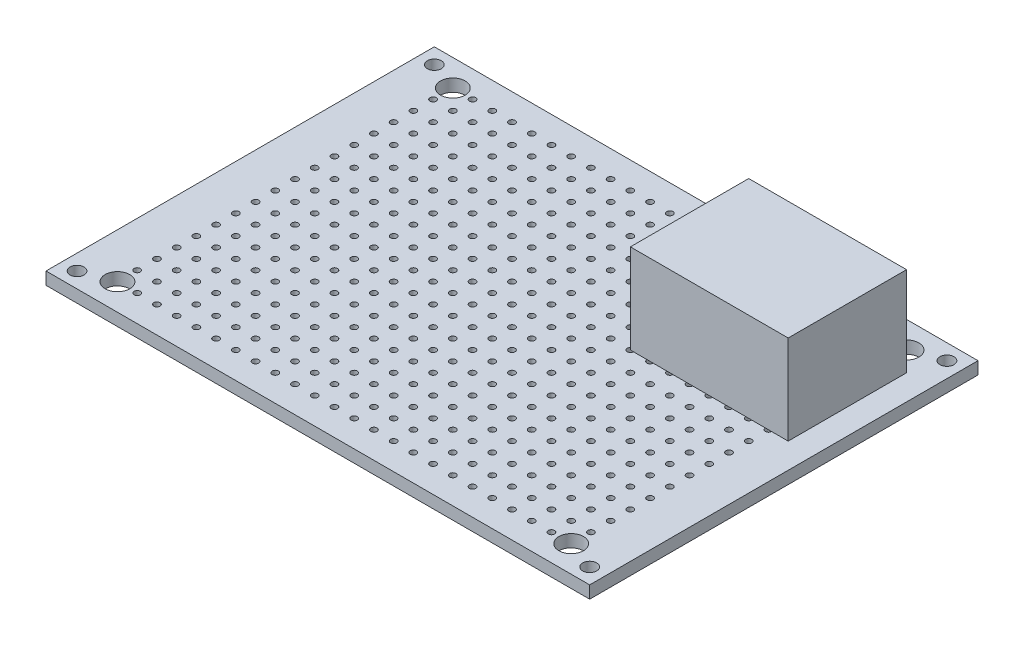
SolidWorks part; units mm, degrees
ref_plane "Front Plane" through (0, 0, 0) normal (0, 0, 1) x (1, 0, 0)
ref_plane "Top Plane" through (0, 0, 0) normal (0, 1, 0) x (1, 0, 0)
ref_plane "Right Plane" through (0, 0, 0) normal (1, 0, 0) x (0, 0, -1)
sketch "Sketch1" plane through (0, 0, 0) normal (0, 1, 0) x (1, 0, 0)
  line L1 (-35, -25) -> (35, -25)
  line L2 (-35, -25) -> (-35, 25)
  line L3 (-35, 25) -> (35, 25)
  line L4 (35, -25) -> (35, 25)
  line L5 (-35, -25) -> (35, 25) construction
  line L6 (-35, 25) -> (35, -25) construction
  point P0 (0, 0)
  dimension "D1" = 50
  dimension "D2" = 70
extrude "Boss-Extrude1" add sketch "Sketch1" along normal blind 1.6
sketch "Sketch2" plane through (0, 1.6, 0) normal (0, 1, 0) x (1, 0, 0)
  line L1 (-33, -23) -> (33, -23) construction
  line L2 (-33, -23) -> (-33, 23) construction
  line L3 (-33, 23) -> (33, 23) construction
  line L4 (33, -23) -> (33, 23) construction
  line L5 (-33, -23) -> (33, 23) construction
  line L6 (-33, 23) -> (33, -23) construction
  circle A0 centre (-33, 23) radius 0.9
  circle A1 centre (-33, -23) radius 0.9
  circle A2 centre (33, -23) radius 0.9
  circle A3 centre (33, 23) radius 0.9
  point P0 (0, 0)
  dimension "D3" = 1.8
  dimension "D1" = 46
  dimension "D2" = 66
extrude "Cut-Extrude1" cut sketch "Sketch2" against normal through all
sketch "Sketch3" plane through (0, 1.6, 0) normal (0, 1, 0) x (1, 0, 0)
  line L0 (-29.21, -21.59) -> (-26.67, -21.59) construction
  line L1 (29.21, -21.59) -> (-29.21, -21.59) construction
  line L2 (29.21, -21.59) -> (29.21, 21.59) construction
  line L3 (29.21, 21.59) -> (-29.21, 21.59) construction
  line L4 (-29.21, -21.59) -> (-29.21, 21.59) construction
  line L5 (29.21, -21.59) -> (-29.21, 21.59) construction
  line L6 (29.21, 21.59) -> (-29.21, -21.59) construction
  line L7 (-29.21, -21.59) -> (-29.21, -19.05) construction
  circle A0 centre (-29.21, -21.59) radius 0.4
  circle A1 centre (-26.67, -21.59) radius 0.4
  circle A2 centre (-24.13, -21.59) radius 0.4
  circle A3 centre (-21.59, -21.59) radius 0.4
  circle A4 centre (-19.05, -21.59) radius 0.4
  circle A5 centre (-16.51, -21.59) radius 0.4
  circle A6 centre (-13.97, -21.59) radius 0.4
  circle A7 centre (-11.43, -21.59) radius 0.4
  circle A8 centre (-8.89, -21.59) radius 0.4
  circle A9 centre (-6.35, -21.59) radius 0.4
  circle A10 centre (-3.81, -21.59) radius 0.4
  circle A11 centre (-1.27, -21.59) radius 0.4
  circle A12 centre (1.27, -21.59) radius 0.4
  circle A13 centre (3.81, -21.59) radius 0.4
  circle A14 centre (6.35, -21.59) radius 0.4
  circle A15 centre (8.89, -21.59) radius 0.4
  circle A16 centre (11.43, -21.59) radius 0.4
  circle A17 centre (13.97, -21.59) radius 0.4
  circle A18 centre (16.51, -21.59) radius 0.4
  circle A19 centre (19.05, -21.59) radius 0.4
  circle A20 centre (21.59, -21.59) radius 0.4
  circle A21 centre (24.13, -21.59) radius 0.4
  circle A22 centre (26.67, -21.59) radius 0.4
  circle A23 centre (29.21, -21.59) radius 0.4
  circle A24 centre (-26.67, -19.05) radius 0.4
  circle A25 centre (-24.13, -19.05) radius 0.4
  circle A26 centre (-21.59, -19.05) radius 0.4
  circle A27 centre (-19.05, -19.05) radius 0.4
  circle A28 centre (-16.51, -19.05) radius 0.4
  circle A29 centre (-13.97, -19.05) radius 0.4
  circle A30 centre (-11.43, -19.05) radius 0.4
  circle A31 centre (-8.89, -19.05) radius 0.4
  circle A32 centre (-6.35, -19.05) radius 0.4
  circle A33 centre (-3.81, -19.05) radius 0.4
  circle A34 centre (-1.27, -19.05) radius 0.4
  circle A35 centre (1.27, -19.05) radius 0.4
  circle A36 centre (3.81, -19.05) radius 0.4
  circle A37 centre (6.35, -19.05) radius 0.4
  circle A38 centre (8.89, -19.05) radius 0.4
  circle A39 centre (11.43, -19.05) radius 0.4
  circle A40 centre (13.97, -19.05) radius 0.4
  circle A41 centre (16.51, -19.05) radius 0.4
  circle A42 centre (19.05, -19.05) radius 0.4
  circle A43 centre (21.59, -19.05) radius 0.4
  circle A44 centre (24.13, -19.05) radius 0.4
  circle A45 centre (26.67, -19.05) radius 0.4
  circle A46 centre (29.21, -19.05) radius 0.4
  circle A47 centre (-26.67, -16.51) radius 0.4
  circle A48 centre (-24.13, -16.51) radius 0.4
  circle A49 centre (-21.59, -16.51) radius 0.4
  circle A50 centre (-19.05, -16.51) radius 0.4
  circle A51 centre (-16.51, -16.51) radius 0.4
  circle A52 centre (-13.97, -16.51) radius 0.4
  circle A53 centre (-11.43, -16.51) radius 0.4
  circle A54 centre (-8.89, -16.51) radius 0.4
  circle A55 centre (-6.35, -16.51) radius 0.4
  circle A56 centre (-3.81, -16.51) radius 0.4
  circle A57 centre (-1.27, -16.51) radius 0.4
  circle A58 centre (1.27, -16.51) radius 0.4
  circle A59 centre (3.81, -16.51) radius 0.4
  circle A60 centre (6.35, -16.51) radius 0.4
  circle A61 centre (8.89, -16.51) radius 0.4
  circle A62 centre (11.43, -16.51) radius 0.4
  circle A63 centre (13.97, -16.51) radius 0.4
  circle A64 centre (16.51, -16.51) radius 0.4
  circle A65 centre (19.05, -16.51) radius 0.4
  circle A66 centre (21.59, -16.51) radius 0.4
  circle A67 centre (24.13, -16.51) radius 0.4
  circle A68 centre (26.67, -16.51) radius 0.4
  circle A69 centre (29.21, -16.51) radius 0.4
  circle A70 centre (-26.67, -13.97) radius 0.4
  circle A71 centre (-24.13, -13.97) radius 0.4
  circle A72 centre (-21.59, -13.97) radius 0.4
  circle A73 centre (-19.05, -13.97) radius 0.4
  circle A74 centre (-16.51, -13.97) radius 0.4
  circle A75 centre (-13.97, -13.97) radius 0.4
  circle A76 centre (-11.43, -13.97) radius 0.4
  circle A77 centre (-8.89, -13.97) radius 0.4
  circle A78 centre (-6.35, -13.97) radius 0.4
  circle A79 centre (-3.81, -13.97) radius 0.4
  circle A80 centre (-1.27, -13.97) radius 0.4
  circle A81 centre (1.27, -13.97) radius 0.4
  circle A82 centre (3.81, -13.97) radius 0.4
  circle A83 centre (6.35, -13.97) radius 0.4
  circle A84 centre (8.89, -13.97) radius 0.4
  circle A85 centre (11.43, -13.97) radius 0.4
  circle A86 centre (13.97, -13.97) radius 0.4
  circle A87 centre (16.51, -13.97) radius 0.4
  circle A88 centre (19.05, -13.97) radius 0.4
  circle A89 centre (21.59, -13.97) radius 0.4
  circle A90 centre (24.13, -13.97) radius 0.4
  circle A91 centre (26.67, -13.97) radius 0.4
  circle A92 centre (29.21, -13.97) radius 0.4
  circle A93 centre (-26.67, -11.43) radius 0.4
  circle A94 centre (-24.13, -11.43) radius 0.4
  circle A95 centre (-21.59, -11.43) radius 0.4
  circle A96 centre (-19.05, -11.43) radius 0.4
  circle A97 centre (-16.51, -11.43) radius 0.4
  circle A98 centre (-13.97, -11.43) radius 0.4
  circle A99 centre (-11.43, -11.43) radius 0.4
  circle A100 centre (-8.89, -11.43) radius 0.4
  circle A101 centre (-6.35, -11.43) radius 0.4
  circle A102 centre (-3.81, -11.43) radius 0.4
  circle A103 centre (-1.27, -11.43) radius 0.4
  circle A104 centre (1.27, -11.43) radius 0.4
  circle A105 centre (3.81, -11.43) radius 0.4
  circle A106 centre (6.35, -11.43) radius 0.4
  circle A107 centre (8.89, -11.43) radius 0.4
  circle A108 centre (11.43, -11.43) radius 0.4
  circle A109 centre (13.97, -11.43) radius 0.4
  circle A110 centre (16.51, -11.43) radius 0.4
  circle A111 centre (19.05, -11.43) radius 0.4
  circle A112 centre (21.59, -11.43) radius 0.4
  circle A113 centre (24.13, -11.43) radius 0.4
  circle A114 centre (26.67, -11.43) radius 0.4
  circle A115 centre (29.21, -11.43) radius 0.4
  circle A116 centre (-26.67, -8.89) radius 0.4
  circle A117 centre (-24.13, -8.89) radius 0.4
  circle A118 centre (-21.59, -8.89) radius 0.4
  circle A119 centre (-19.05, -8.89) radius 0.4
  circle A120 centre (-16.51, -8.89) radius 0.4
  circle A121 centre (-13.97, -8.89) radius 0.4
  circle A122 centre (-11.43, -8.89) radius 0.4
  circle A123 centre (-8.89, -8.89) radius 0.4
  circle A124 centre (-6.35, -8.89) radius 0.4
  circle A125 centre (-3.81, -8.89) radius 0.4
  circle A126 centre (-1.27, -8.89) radius 0.4
  circle A127 centre (1.27, -8.89) radius 0.4
  circle A128 centre (3.81, -8.89) radius 0.4
  circle A129 centre (6.35, -8.89) radius 0.4
  circle A130 centre (8.89, -8.89) radius 0.4
  circle A131 centre (11.43, -8.89) radius 0.4
  circle A132 centre (13.97, -8.89) radius 0.4
  circle A133 centre (16.51, -8.89) radius 0.4
  circle A134 centre (19.05, -8.89) radius 0.4
  circle A135 centre (21.59, -8.89) radius 0.4
  circle A136 centre (24.13, -8.89) radius 0.4
  circle A137 centre (26.67, -8.89) radius 0.4
  circle A138 centre (29.21, -8.89) radius 0.4
  circle A139 centre (-26.67, -6.35) radius 0.4
  circle A140 centre (-24.13, -6.35) radius 0.4
  circle A141 centre (-21.59, -6.35) radius 0.4
  circle A142 centre (-19.05, -6.35) radius 0.4
  circle A143 centre (-16.51, -6.35) radius 0.4
  circle A144 centre (-13.97, -6.35) radius 0.4
  circle A145 centre (-11.43, -6.35) radius 0.4
  circle A146 centre (-8.89, -6.35) radius 0.4
  circle A147 centre (-6.35, -6.35) radius 0.4
  circle A148 centre (-3.81, -6.35) radius 0.4
  circle A149 centre (-1.27, -6.35) radius 0.4
  circle A150 centre (1.27, -6.35) radius 0.4
  circle A151 centre (3.81, -6.35) radius 0.4
  circle A152 centre (6.35, -6.35) radius 0.4
  circle A153 centre (8.89, -6.35) radius 0.4
  circle A154 centre (11.43, -6.35) radius 0.4
  circle A155 centre (13.97, -6.35) radius 0.4
  circle A156 centre (16.51, -6.35) radius 0.4
  circle A157 centre (19.05, -6.35) radius 0.4
  circle A158 centre (21.59, -6.35) radius 0.4
  circle A159 centre (24.13, -6.35) radius 0.4
  circle A160 centre (26.67, -6.35) radius 0.4
  circle A161 centre (29.21, -6.35) radius 0.4
  circle A162 centre (-26.67, -3.81) radius 0.4
  circle A163 centre (-24.13, -3.81) radius 0.4
  circle A164 centre (-21.59, -3.81) radius 0.4
  circle A165 centre (-19.05, -3.81) radius 0.4
  circle A166 centre (-16.51, -3.81) radius 0.4
  circle A167 centre (-13.97, -3.81) radius 0.4
  circle A168 centre (-11.43, -3.81) radius 0.4
  circle A169 centre (-8.89, -3.81) radius 0.4
  circle A170 centre (-6.35, -3.81) radius 0.4
  circle A171 centre (-3.81, -3.81) radius 0.4
  circle A172 centre (-1.27, -3.81) radius 0.4
  circle A173 centre (1.27, -3.81) radius 0.4
  circle A174 centre (3.81, -3.81) radius 0.4
  circle A175 centre (6.35, -3.81) radius 0.4
  circle A176 centre (8.89, -3.81) radius 0.4
  circle A177 centre (11.43, -3.81) radius 0.4
  circle A178 centre (13.97, -3.81) radius 0.4
  circle A179 centre (16.51, -3.81) radius 0.4
  circle A180 centre (19.05, -3.81) radius 0.4
  circle A181 centre (21.59, -3.81) radius 0.4
  circle A182 centre (24.13, -3.81) radius 0.4
  circle A183 centre (26.67, -3.81) radius 0.4
  circle A184 centre (29.21, -3.81) radius 0.4
  circle A185 centre (-26.67, -1.27) radius 0.4
  circle A186 centre (-24.13, -1.27) radius 0.4
  circle A187 centre (-21.59, -1.27) radius 0.4
  circle A188 centre (-19.05, -1.27) radius 0.4
  circle A189 centre (-16.51, -1.27) radius 0.4
  circle A190 centre (-13.97, -1.27) radius 0.4
  circle A191 centre (-11.43, -1.27) radius 0.4
  circle A192 centre (-8.89, -1.27) radius 0.4
  circle A193 centre (-6.35, -1.27) radius 0.4
  circle A194 centre (-3.81, -1.27) radius 0.4
  circle A195 centre (-1.27, -1.27) radius 0.4
  circle A196 centre (1.27, -1.27) radius 0.4
  circle A197 centre (3.81, -1.27) radius 0.4
  circle A198 centre (6.35, -1.27) radius 0.4
  circle A199 centre (8.89, -1.27) radius 0.4
  circle A200 centre (11.43, -1.27) radius 0.4
  circle A201 centre (13.97, -1.27) radius 0.4
  circle A202 centre (16.51, -1.27) radius 0.4
  circle A203 centre (19.05, -1.27) radius 0.4
  circle A204 centre (21.59, -1.27) radius 0.4
  circle A205 centre (24.13, -1.27) radius 0.4
  circle A206 centre (26.67, -1.27) radius 0.4
  circle A207 centre (29.21, -1.27) radius 0.4
  circle A208 centre (-26.67, 1.27) radius 0.4
  circle A209 centre (-24.13, 1.27) radius 0.4
  circle A210 centre (-21.59, 1.27) radius 0.4
  circle A211 centre (-19.05, 1.27) radius 0.4
  circle A212 centre (-16.51, 1.27) radius 0.4
  circle A213 centre (-13.97, 1.27) radius 0.4
  circle A214 centre (-11.43, 1.27) radius 0.4
  circle A215 centre (-8.89, 1.27) radius 0.4
  circle A216 centre (-6.35, 1.27) radius 0.4
  circle A217 centre (-3.81, 1.27) radius 0.4
  circle A218 centre (-1.27, 1.27) radius 0.4
  circle A219 centre (1.27, 1.27) radius 0.4
  circle A220 centre (3.81, 1.27) radius 0.4
  circle A221 centre (6.35, 1.27) radius 0.4
  circle A222 centre (8.89, 1.27) radius 0.4
  circle A223 centre (11.43, 1.27) radius 0.4
  circle A224 centre (13.97, 1.27) radius 0.4
  circle A225 centre (16.51, 1.27) radius 0.4
  circle A226 centre (19.05, 1.27) radius 0.4
  circle A227 centre (21.59, 1.27) radius 0.4
  circle A228 centre (24.13, 1.27) radius 0.4
  circle A229 centre (26.67, 1.27) radius 0.4
  circle A230 centre (29.21, 1.27) radius 0.4
  circle A231 centre (-26.67, 3.81) radius 0.4
  circle A232 centre (-24.13, 3.81) radius 0.4
  circle A233 centre (-21.59, 3.81) radius 0.4
  circle A234 centre (-19.05, 3.81) radius 0.4
  circle A235 centre (-16.51, 3.81) radius 0.4
  circle A236 centre (-13.97, 3.81) radius 0.4
  circle A237 centre (-11.43, 3.81) radius 0.4
  circle A238 centre (-8.89, 3.81) radius 0.4
  circle A239 centre (-6.35, 3.81) radius 0.4
  circle A240 centre (-3.81, 3.81) radius 0.4
  circle A241 centre (-1.27, 3.81) radius 0.4
  circle A242 centre (1.27, 3.81) radius 0.4
  circle A243 centre (3.81, 3.81) radius 0.4
  circle A244 centre (6.35, 3.81) radius 0.4
  circle A245 centre (8.89, 3.81) radius 0.4
  circle A246 centre (11.43, 3.81) radius 0.4
  circle A247 centre (13.97, 3.81) radius 0.4
  circle A248 centre (16.51, 3.81) radius 0.4
  circle A249 centre (19.05, 3.81) radius 0.4
  circle A250 centre (21.59, 3.81) radius 0.4
  circle A251 centre (24.13, 3.81) radius 0.4
  circle A252 centre (26.67, 3.81) radius 0.4
  circle A253 centre (29.21, 3.81) radius 0.4
  circle A254 centre (-26.67, 6.35) radius 0.4
  circle A255 centre (-24.13, 6.35) radius 0.4
  circle A256 centre (-21.59, 6.35) radius 0.4
  circle A257 centre (-19.05, 6.35) radius 0.4
  circle A258 centre (-16.51, 6.35) radius 0.4
  circle A259 centre (-13.97, 6.35) radius 0.4
  circle A260 centre (-11.43, 6.35) radius 0.4
  circle A261 centre (-8.89, 6.35) radius 0.4
  circle A262 centre (-6.35, 6.35) radius 0.4
  circle A263 centre (-3.81, 6.35) radius 0.4
  circle A264 centre (-1.27, 6.35) radius 0.4
  circle A265 centre (1.27, 6.35) radius 0.4
  circle A266 centre (3.81, 6.35) radius 0.4
  circle A267 centre (6.35, 6.35) radius 0.4
  circle A268 centre (8.89, 6.35) radius 0.4
  circle A269 centre (11.43, 6.35) radius 0.4
  circle A270 centre (13.97, 6.35) radius 0.4
  circle A271 centre (16.51, 6.35) radius 0.4
  circle A272 centre (19.05, 6.35) radius 0.4
  circle A273 centre (21.59, 6.35) radius 0.4
  circle A274 centre (24.13, 6.35) radius 0.4
  circle A275 centre (26.67, 6.35) radius 0.4
  circle A276 centre (29.21, 6.35) radius 0.4
  circle A277 centre (-26.67, 8.89) radius 0.4
  circle A278 centre (-24.13, 8.89) radius 0.4
  circle A279 centre (-21.59, 8.89) radius 0.4
  circle A280 centre (-19.05, 8.89) radius 0.4
  circle A281 centre (-16.51, 8.89) radius 0.4
  circle A282 centre (-13.97, 8.89) radius 0.4
  circle A283 centre (-11.43, 8.89) radius 0.4
  circle A284 centre (-8.89, 8.89) radius 0.4
  circle A285 centre (-6.35, 8.89) radius 0.4
  circle A286 centre (-3.81, 8.89) radius 0.4
  circle A287 centre (-1.27, 8.89) radius 0.4
  circle A288 centre (1.27, 8.89) radius 0.4
  circle A289 centre (3.81, 8.89) radius 0.4
  circle A290 centre (6.35, 8.89) radius 0.4
  circle A291 centre (8.89, 8.89) radius 0.4
  circle A292 centre (11.43, 8.89) radius 0.4
  circle A293 centre (13.97, 8.89) radius 0.4
  circle A294 centre (16.51, 8.89) radius 0.4
  circle A295 centre (19.05, 8.89) radius 0.4
  circle A296 centre (21.59, 8.89) radius 0.4
  circle A297 centre (24.13, 8.89) radius 0.4
  circle A298 centre (26.67, 8.89) radius 0.4
  circle A299 centre (29.21, 8.89) radius 0.4
  circle A300 centre (-26.67, 11.43) radius 0.4
  circle A301 centre (-24.13, 11.43) radius 0.4
  circle A302 centre (-21.59, 11.43) radius 0.4
  circle A303 centre (-19.05, 11.43) radius 0.4
  circle A304 centre (-16.51, 11.43) radius 0.4
  circle A305 centre (-13.97, 11.43) radius 0.4
  circle A306 centre (-11.43, 11.43) radius 0.4
  circle A307 centre (-8.89, 11.43) radius 0.4
  circle A308 centre (-6.35, 11.43) radius 0.4
  circle A309 centre (-3.81, 11.43) radius 0.4
  circle A310 centre (-1.27, 11.43) radius 0.4
  circle A311 centre (1.27, 11.43) radius 0.4
  circle A312 centre (3.81, 11.43) radius 0.4
  circle A313 centre (6.35, 11.43) radius 0.4
  circle A314 centre (8.89, 11.43) radius 0.4
  circle A315 centre (11.43, 11.43) radius 0.4
  circle A316 centre (13.97, 11.43) radius 0.4
  circle A317 centre (16.51, 11.43) radius 0.4
  circle A318 centre (19.05, 11.43) radius 0.4
  circle A319 centre (21.59, 11.43) radius 0.4
  circle A320 centre (24.13, 11.43) radius 0.4
  circle A321 centre (26.67, 11.43) radius 0.4
  circle A322 centre (29.21, 11.43) radius 0.4
  circle A323 centre (-26.67, 13.97) radius 0.4
  circle A324 centre (-24.13, 13.97) radius 0.4
  circle A325 centre (-21.59, 13.97) radius 0.4
  circle A326 centre (-19.05, 13.97) radius 0.4
  circle A327 centre (-16.51, 13.97) radius 0.4
  circle A328 centre (-13.97, 13.97) radius 0.4
  circle A329 centre (-11.43, 13.97) radius 0.4
  circle A330 centre (-8.89, 13.97) radius 0.4
  circle A331 centre (-6.35, 13.97) radius 0.4
  circle A332 centre (-3.81, 13.97) radius 0.4
  circle A333 centre (-1.27, 13.97) radius 0.4
  circle A334 centre (1.27, 13.97) radius 0.4
  circle A335 centre (3.81, 13.97) radius 0.4
  circle A336 centre (6.35, 13.97) radius 0.4
  circle A337 centre (8.89, 13.97) radius 0.4
  circle A338 centre (11.43, 13.97) radius 0.4
  circle A339 centre (13.97, 13.97) radius 0.4
  circle A340 centre (16.51, 13.97) radius 0.4
  circle A341 centre (19.05, 13.97) radius 0.4
  circle A342 centre (21.59, 13.97) radius 0.4
  circle A343 centre (24.13, 13.97) radius 0.4
  circle A344 centre (26.67, 13.97) radius 0.4
  circle A345 centre (29.21, 13.97) radius 0.4
  circle A346 centre (-26.67, 16.51) radius 0.4
  circle A347 centre (-24.13, 16.51) radius 0.4
  circle A348 centre (-21.59, 16.51) radius 0.4
  circle A349 centre (-19.05, 16.51) radius 0.4
  circle A350 centre (-16.51, 16.51) radius 0.4
  circle A351 centre (-13.97, 16.51) radius 0.4
  circle A352 centre (-11.43, 16.51) radius 0.4
  circle A353 centre (-8.89, 16.51) radius 0.4
  circle A354 centre (-6.35, 16.51) radius 0.4
  circle A355 centre (-3.81, 16.51) radius 0.4
  circle A356 centre (-1.27, 16.51) radius 0.4
  circle A357 centre (1.27, 16.51) radius 0.4
  circle A358 centre (3.81, 16.51) radius 0.4
  circle A359 centre (6.35, 16.51) radius 0.4
  circle A360 centre (8.89, 16.51) radius 0.4
  circle A361 centre (11.43, 16.51) radius 0.4
  circle A362 centre (13.97, 16.51) radius 0.4
  circle A363 centre (16.51, 16.51) radius 0.4
  circle A364 centre (19.05, 16.51) radius 0.4
  circle A365 centre (21.59, 16.51) radius 0.4
  circle A366 centre (24.13, 16.51) radius 0.4
  circle A367 centre (26.67, 16.51) radius 0.4
  circle A368 centre (29.21, 16.51) radius 0.4
  circle A369 centre (-26.67, 19.05) radius 0.4
  circle A370 centre (-24.13, 19.05) radius 0.4
  circle A371 centre (-21.59, 19.05) radius 0.4
  circle A372 centre (-19.05, 19.05) radius 0.4
  circle A373 centre (-16.51, 19.05) radius 0.4
  circle A374 centre (-13.97, 19.05) radius 0.4
  circle A375 centre (-11.43, 19.05) radius 0.4
  circle A376 centre (-8.89, 19.05) radius 0.4
  circle A377 centre (-6.35, 19.05) radius 0.4
  circle A378 centre (-3.81, 19.05) radius 0.4
  circle A379 centre (-1.27, 19.05) radius 0.4
  circle A380 centre (1.27, 19.05) radius 0.4
  circle A381 centre (3.81, 19.05) radius 0.4
  circle A382 centre (6.35, 19.05) radius 0.4
  circle A383 centre (8.89, 19.05) radius 0.4
  circle A384 centre (11.43, 19.05) radius 0.4
  circle A385 centre (13.97, 19.05) radius 0.4
  circle A386 centre (16.51, 19.05) radius 0.4
  circle A387 centre (19.05, 19.05) radius 0.4
  circle A388 centre (21.59, 19.05) radius 0.4
  circle A389 centre (24.13, 19.05) radius 0.4
  circle A390 centre (26.67, 19.05) radius 0.4
  circle A391 centre (29.21, 19.05) radius 0.4
  circle A392 centre (-26.67, 21.59) radius 0.4
  circle A393 centre (-24.13, 21.59) radius 0.4
  circle A394 centre (-21.59, 21.59) radius 0.4
  circle A395 centre (-19.05, 21.59) radius 0.4
  circle A396 centre (-16.51, 21.59) radius 0.4
  circle A397 centre (-13.97, 21.59) radius 0.4
  circle A398 centre (-11.43, 21.59) radius 0.4
  circle A399 centre (-8.89, 21.59) radius 0.4
  circle A400 centre (-6.35, 21.59) radius 0.4
  circle A401 centre (-3.81, 21.59) radius 0.4
  circle A402 centre (-1.27, 21.59) radius 0.4
  circle A403 centre (1.27, 21.59) radius 0.4
  circle A404 centre (3.81, 21.59) radius 0.4
  circle A405 centre (6.35, 21.59) radius 0.4
  circle A406 centre (8.89, 21.59) radius 0.4
  circle A407 centre (11.43, 21.59) radius 0.4
  circle A408 centre (13.97, 21.59) radius 0.4
  circle A409 centre (16.51, 21.59) radius 0.4
  circle A410 centre (19.05, 21.59) radius 0.4
  circle A411 centre (21.59, 21.59) radius 0.4
  circle A412 centre (24.13, 21.59) radius 0.4
  circle A413 centre (26.67, 21.59) radius 0.4
  circle A414 centre (29.21, 21.59) radius 0.4
  circle A415 centre (-29.21, -19.05) radius 0.4
  circle A416 centre (-29.21, -16.51) radius 0.4
  circle A417 centre (-29.21, -13.97) radius 0.4
  circle A418 centre (-29.21, -11.43) radius 0.4
  circle A419 centre (-29.21, -8.89) radius 0.4
  circle A420 centre (-29.21, -6.35) radius 0.4
  circle A421 centre (-29.21, -3.81) radius 0.4
  circle A422 centre (-29.21, -1.27) radius 0.4
  circle A423 centre (-29.21, 1.27) radius 0.4
  circle A424 centre (-29.21, 3.81) radius 0.4
  circle A425 centre (-29.21, 6.35) radius 0.4
  circle A426 centre (-29.21, 8.89) radius 0.4
  circle A427 centre (-29.21, 11.43) radius 0.4
  circle A428 centre (-29.21, 13.97) radius 0.4
  circle A429 centre (-29.21, 16.51) radius 0.4
  circle A430 centre (-29.21, 19.05) radius 0.4
  circle A431 centre (-29.21, 21.59) radius 0.4
  point P0 (0, 0)
  point P3 (0, 0)
  point P7 (0, 0)
  point P8 (26.9732, 24.3534)
  point P9 (0, 0)
  point P875 (0, 0)
  dimension "D1" = 0.8
  dimension "D4" = 90
  dimension "D5" = 2.54
  dimension "D6" = 2.54
  dimension "D2" = 24
  dimension "D3" = 18
extrude "Cut-Extrude2" cut sketch "Sketch3" against normal through all
sketch "Sketch4" plane through (0, 1.6, 0) normal (0, 1, 0) x (1, 0, 0)
  circle A0 centre (-29.21, 21.59) radius 1.5875
  circle A1 centre (29.21, 21.59) radius 1.5875
  circle A2 centre (29.21, -21.59) radius 1.5875
  circle A3 centre (-29.21, -21.59) radius 1.5875
  dimension "D1" = 3.175
extrude "Cut-Extrude3" cut sketch "Sketch4" against normal through all
ref_plane "Plane1" through (0, 0, 0) normal (-1, 0, 0) x (0, 0, 1)
sketch "Sketch5" plane through (0, 1.6, 0) normal (0, 1, 0) x (1, 0, 0)
  line L1 (11.43, 3.81) -> (31.75, 3.81)
  line L2 (11.43, 3.81) -> (11.43, 19.05)
  line L3 (11.43, 19.05) -> (31.75, 19.05)
  line L4 (31.75, 3.81) -> (31.75, 19.05)
  line L5 (11.43, 3.81) -> (31.75, 19.05) construction
  line L6 (11.43, 19.05) -> (31.75, 3.81) construction
  point P0 (21.59, 11.43)
  point P5 (21.59, 11.43)
  point P6 (0, 0)
  point P8 (11.43, 19.05)
extrude "Boss-Extrude2" add sketch "Sketch5" along normal blind 11.5 separate body
